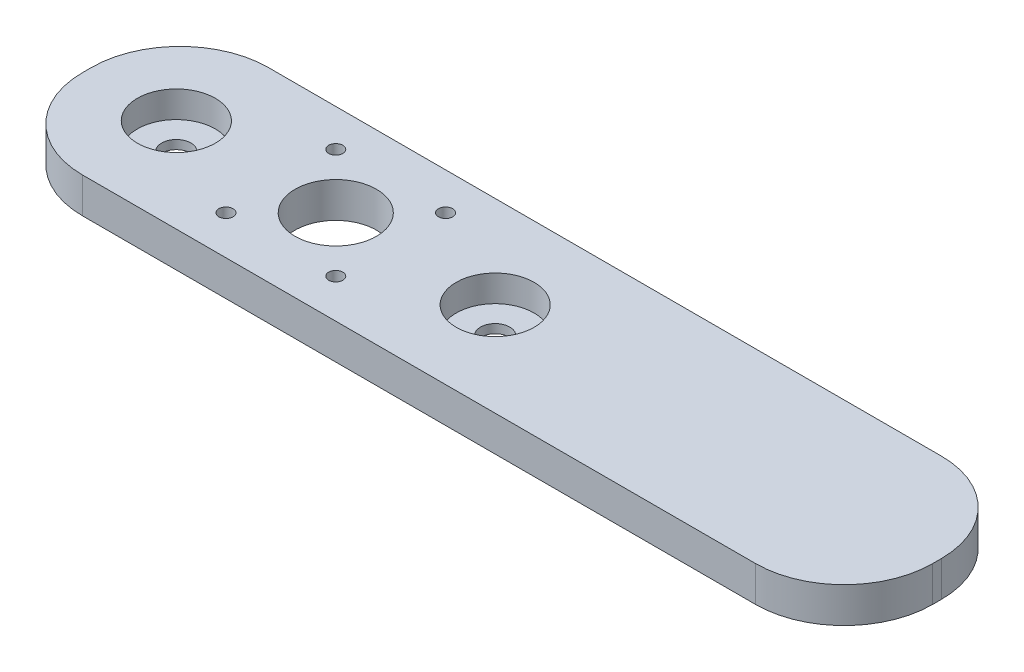
SolidWorks part; units mm, degrees
ref_plane "Front Plane" through (0, 0, 0) normal (0, 0, 1) x (1, 0, 0)
ref_plane "Top Plane" through (0, 0, 0) normal (0, 1, 0) x (1, 0, 0)
ref_plane "Right Plane" through (0, 0, 0) normal (1, 0, 0) x (0, 0, -1)
sketch "Sketch1" plane through (0, 0, 0) normal (0, 1, 0) x (1, 0, 0)
  line L0 (-45, -27) -> (-25, -27)
  line L1 (-70, 0) -> (-70, -2)
  line L2 (45, -27) -> (70, -27)
  line L3 (-25, -27) -> (25, -27)
  line L4 (70, -27) -> (70, -2)
  line L5 (-45, 25) -> (45, 25)
  line L6 (70, 0) -> (70, -2)
  line L7 (45, -27) -> (25, -27)
  line L8 (0, 25) -> (0, -27) construction
  line L9 (-45, -27) -> (-70, -27)
  line L10 (-70, -27) -> (-70, -2)
  circle A0 centre (-45, 0) radius 11
  arc A1 (-45, 25) -> (-70, 0) centre (-45, 0) ccw
  circle A3 centre (0, 0) radius 22 construction
  arc A4 (45, 25) -> (70, 0) centre (45, 0) cw
  circle A5 centre (45, 0) radius 11
  point P17 (70, 25)
  point P33 (-70, -27)
  point P36 (70, -27)
  dimension "D1" = 44
  dimension "D4" = 25
extrude "Boss-Extrude1" add sketch "Sketch1" along normal blind 10
sketch "Sketch2" plane through (0, 0, 0) normal (0, -1, 0) x (1, 0, 0)
  circle A0 centre (-45, 0) radius 4.125
  circle A1 centre (45, 0) radius 4.125
  circle A2 centre (45, 0) radius 11
  circle A3 centre (-45, 0) radius 11
  dimension "D1" = 8.25
  dimension "D2" = 8.25
  dimension "D3" = 22
  dimension "D4" = 22
extrude "Boss-Extrude2" add sketch "Sketch2" against normal blind 2.5
sketch "Sketch4" plane through (0, 10, 0) normal (0, 1, 0) x (1, 0, 0)
  line L0 (-20.15, -16.7358) -> (-16.7358, -20.15) construction
  line L1 (-16.7358, -20.15) -> (16.7358, -20.15) construction
  line L2 (16.7358, -20.15) -> (20.15, -16.7358) construction
  line L3 (20.15, -16.7358) -> (20.15, 16.7358) construction
  line L4 (20.15, 16.7358) -> (16.7358, 20.15) construction
  line L5 (16.7358, 20.15) -> (-16.7358, 20.15) construction
  line L6 (-16.7358, 20.15) -> (-20.15, 16.7358) construction
  line L7 (-20.15, 16.7358) -> (-20.15, -16.7358) construction
  circle A0 centre (15.5, 15.5) radius 2
  circle A1 centre (-15.5, 15.5) radius 2
  circle A2 centre (-15.5, -15.5) radius 2
  circle A3 centre (15.5, -15.5) radius 2
  circle A4 centre (0, 0) radius 11.5
extrude "Cut-Extrude1" cut sketch "Sketch4" against normal blind 10
sketch "Sketch5" plane through (0, 0, 0) normal (0, -1, 0) x (-1, 0, 0)
  line L0 (-70, -27) -> (-151.3735, -27)
  line L1 (-151.3735, -27) -> (-151.3735, 25)
  line L2 (-151.3735, 25) -> (-45, 25)
  line L3 (-45, 25) -> (-50.9868, 16.3149)
  line L4 (-50.9868, 16.3149) -> (-65.4458, 2.6821)
  line L5 (-65.4458, 2.6821) -> (-66.1392, -20.8936)
  line L6 (-66.1392, -20.8936) -> (-70, -27)
extrude "Boss-Extrude3" add sketch "Sketch5" against normal blind 10
sketch "Sketch6" plane through (0, 0, 0) normal (0, -1, 0) x (-1, 0, 0)
  line L0 (70, -27) -> (-170, -27) construction
  line L1 (-151.3735, 25) -> (-170, 25)
  line L2 (-170, 25) -> (-170, -27)
  line L3 (-170, -27) -> (-151.3735, -27)
  line L4 (-151.3735, -27) -> (-141.0383, -1)
  line L5 (-141.0383, -1) -> (-151.3735, 25)
  dimension "D1" = 240
extrude "Boss-Extrude4" add sketch "Sketch6" against normal blind 10
fillet "Fillet1" radius 25 3 edges at (170, 5, -25) (170, 5, 27) (-70, 5, 27)
sketch "Sketch7" plane through (0, 10, 0) normal (0, 1, 0) x (1, 0, 0)
  line L0 (165.3678, -26) -> (133.9806, -69.2977)
  line L1 (-328.7473, 26) -> (188.7473, 26)
  line L2 (-328.7473, 26) -> (-328.7473, -26)
  line L3 (-328.7473, -26) -> (188.7473, -26)
  line L4 (188.7473, 26) -> (188.7473, -26)
  line L5 (-328.7473, 26) -> (188.7473, -26) construction
  line L6 (-328.7473, -26) -> (188.7473, 26) construction
  line L7 (133.9806, -69.2977) -> (-45.1107, -66.5282)
  line L8 (-45.1107, -66.5282) -> (-59.2657, -26)
  point P0 (-70, 0)
  arc M7 (-70, -2) -> (-45, -27) centre (-45, -2) ccw
  line M8 (-45, -27) -> (145, -27)
  arc M9 (145, -27) -> (170, -2) centre (145, -2) ccw
  dimension "D1" = 52
extrude "Cut-Extrude5" cut sketch "Sketch7" against normal blind 10 contours L8 L7 L0 L3 M9 M8 M7 | L3 M7 M8 M9
sketch "Sketch10" plane through (0, 10, 0) normal (0, 1, 0) x (1, 0, 0)
  line L0 (170, 0) -> (55.5983, 15.9528)
  line L1 (170, 0) -> (-70, 0)
  line L2 (170, 0) -> (170, -26)
  line L3 (170, -26) -> (-70, -26)
  line L4 (-70, 0) -> (-70, -26)
  line L5 (170, 0) -> (-70, 0)
  line L6 (170, 0) -> (170, 26)
  line L7 (170, 26) -> (-70, 26)
  line L8 (-70, 0) -> (-70, 26)
  line L9 (55.5983, 15.9528) -> (0, 23.7057)
  line L10 (0, 23.7057) -> (-30.2305, 19.8293)
  line L11 (-30.2305, 19.8293) -> (-63.9073, 7.9764)
  line L12 (-63.9073, 7.9764) -> (-70, 0)
  arc M20 (170, 0) -> (145, 25) centre (145, 0) ccw
  line M21 (145, 25) -> (-45, 25)
  arc M22 (-45, 25) -> (-70, 0) centre (-45, 0) ccw
  dimension "D1" = 26
  dimension "D2" = 26
extrude "Boss-Extrude6" add sketch "Sketch10" against normal blind 10 contours L12 L11 L10 L9 L0 M20 M21 M22 | L8 L6 L7 M22 M21 M20
fillet "Fillet3" radius 25 2 edges at (-70, 5, -26) (170, 5, -26)
sketch "Sketch11" plane through (0, 10, 0) normal (0, 1, 0) x (1, 0, 0)
  line L0 (170, 1) -> (170, -2) construction
  line L1 (170, -0.5) -> (-70, -0.5)
  line L2 (170, -0.5) -> (170, -26.5)
  line L3 (170, -26.5) -> (-70, -26.5)
  line L4 (-70, -0.5) -> (-70, -26.5)
  line L5 (170, -0.5) -> (142.4378, -19.8319)
  line L6 (-70, -0.5) -> (170, -0.5)
  line L7 (-70, -0.5) -> (-70, 25.5)
  line L8 (-70, 25.5) -> (170, 25.5)
  line L9 (170, -0.5) -> (170, 25.5)
  line L10 (142.4378, -19.8319) -> (-54.3303, -19.8319)
  line L11 (-54.3303, -19.8319) -> (-70, -0.5)
  line M5 (-70, 1) -> (-70, -2)
  arc M6 (-70, -2) -> (-52, -26) centre (-45, -2) ccw
  line M7 (-52, -26) -> (152, -26)
  arc M8 (152, -26) -> (170, -2) centre (145, -2) ccw
  line M9 (170, -2) -> (170, 1)
  dimension "D1" = 26
  dimension "D2" = 26
extrude "Boss-Extrude7" add sketch "Sketch11" against normal blind 10 contours L10 L11 L5 M5 M6 M7 M8 M9 | L4 L3 L2 M6 M8 M7
fillet "Fillet4" radius 25 2 edges at (-70, 5, 26.5) (170, 5, 26.5)
